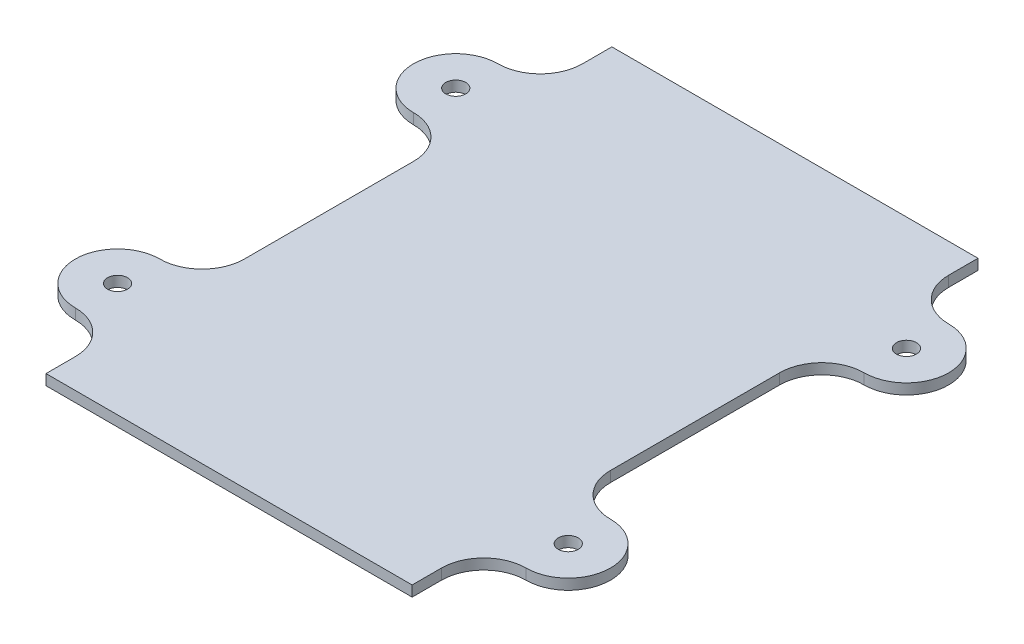
SolidWorks part; units mm, degrees
ref_plane "Front Plane" through (0, 0, 0) normal (0, 0, 1) x (1, 0, 0)
ref_plane "Top Plane" through (0, 0, 0) normal (0, 1, 0) x (1, 0, 0)
ref_plane "Right Plane" through (0, 0, 0) normal (1, 0, 0) x (0, 0, -1)
sketch "Sketch1" plane through (0, 0, 0) normal (0, 1, 0) x (1, 0, 0)
  line L0 (33.85, 25.4) -> (27.5, 25.4) construction
  line L1 (-27.5, -42.5) -> (27.5, -42.5)
  line L2 (-27.5, -42.5) -> (-27.5, 42.5)
  line L3 (-27.5, 42.5) -> (27.5, 42.5)
  line L4 (27.5, -42.5) -> (27.5, 12.7)
  line L5 (-27.5, -42.5) -> (27.5, 42.5) construction
  line L6 (-27.5, 42.5) -> (27.5, -42.5) construction
  line L7 (27.5, 38.1) -> (27.5, 42.5)
  arc A0 (33.85, 31.75) -> (33.85, 19.05) centre (33.85, 25.4) cw
  arc A1 (33.85, 31.75) -> (27.5, 38.1) centre (33.85, 38.1) cw
  arc A2 (33.85, 19.05) -> (27.5, 12.7) centre (33.85, 12.7) ccw
  circle A3 centre (33.85, 25.4) radius 1.5
  point P0 (0, 0)
  point P13 (33.6357, 35.0859)
  point P15 (27.5, 39.6364)
  point P16 (34.2858, 19.3106)
  point P17 (33.85, 12.8532)
  point P18 (33.85, 32.3122)
  point P20 (0, 0)
  dimension "D3" = 3
  dimension "D4" = 6.35
  dimension "D5" = 25.4
  dimension "D1" = 55
  dimension "D2" = 85
extrude "Boss-Extrude1" add sketch "Sketch1" along normal blind 1.5875
mirror "Mirror1" about plane through (0, 0, 0) normal (0, 0, 1) of "Boss-Extrude1"
mirror "Mirror2" about plane through (0, 0, 0) normal (1, 0, 0) of "Mirror1", "Boss-Extrude1"
